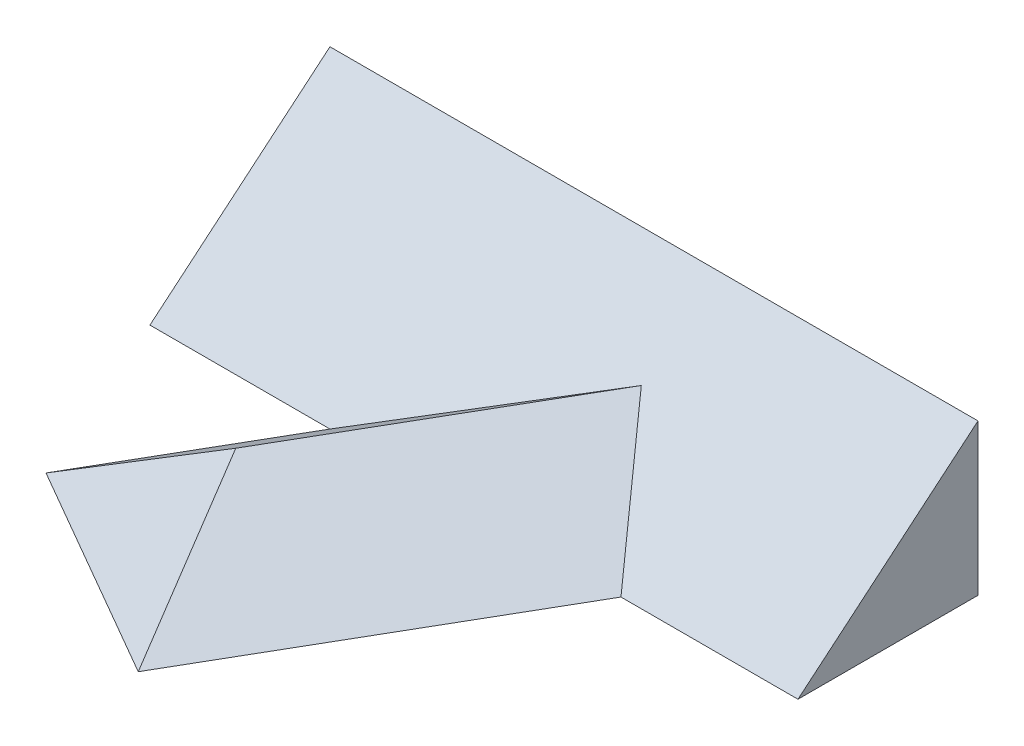
SolidWorks part; units mm, degrees
ref_plane "Front" through (0, 0, 0) normal (0, 0, 1) x (1, 0, 0)
ref_plane "Top" through (0, 0, 0) normal (0, 1, 0) x (1, 0, 0)
ref_plane "Right" through (0, 0, 0) normal (1, 0, 0) x (0, 0, -1)
sketch "Sketch1" plane through (0, 0, 0) normal (1, 0, 0) x (0, 0, -1)
  line L0 (0, 0) -> (50, 0)
  line L1 (50, 0) -> (50, 41.955)
  line L2 (50, 41.955) -> (0, 0)
  dimension "D1" = 50
  dimension "D2" = 40
extrude "Extrude1" add sketch "Sketch1" along normal blind 180
sketch "Sketch2" plane through (0, 0, 0) normal (0, 1, 0) x (1, 0, 0)
  line L0 (50, 50) -> (50, -28.1305) construction
  line L1 (180, 50) -> (0, 50) construction
  line L2 (0, 50) -> (0, 0) construction
  line L3 (50, 0) -> (10.2784, -68.7999) construction
  line L4 (180, 0) -> (0, 0) construction
  line L5 (11.5393, -44.4614) -> (81.7543, -85) construction
  line L6 (81.7543, -85) -> (130.829, 0) construction
  point P14 (21.1325, -50)
  dimension "D1" = 50
  dimension "D2" = 60
  dimension "D3" = 50
ref_plane "Plane3" through (0, 0, 50) normal (0, 0, 1) x (1, 0, 0)
sketch "Sketch4" plane through (0, 0, 50) normal (0, 0, 1) x (1, 0, 0)
  point P0 (21.1325, 31.1469)
ref_plane "Plane4" through (-16.3675, 0, 28.3494) normal (-0.5, 0, 0.866) x (0.866, 0, 0.5)
sketch "Sketch5" plane through (-16.3675, 0, 28.3494) normal (-0.5, 0, 0.866) x (0.866, 0, 0.5)
  line L0 (43.3013, 0) -> (78.3013, 24.5073)
  line L1 (78.3013, 24.5073) -> (113.3013, 0)
  line L2 (155.8846, 0) -> (0, 0) construction
  line L3 (113.3013, 0) -> (43.3013, 0)
  dimension "D1" = 70
  dimension "D2" = 35
  dimension "D3" = 35
extrude "Extrude2" add sketch "Sketch5" against normal blind 115
ref_plane "Plane5" through (51.4434, 0, 67.5) normal (0.866, 0, 0.5) x (0.5, 0, -0.866)
sketch "Sketch6" plane through (51.4434, 0, 67.5) normal (0.866, 0, 0.5) x (0.5, 0, -0.866)
  line L0 (29.2066, 24.5073) -> (0, 24.5073)
  line L1 (111.6672, 24.5073) -> (0, 24.5073) construction
  line L2 (0, 24.5073) -> (0, 0)
  line L3 (0, 0) -> (29.2066, 24.5073)
  line L4 (98.1495, 0) -> (0, 0) construction
  dimension "D1" = 40
extrude "Cut-Extrude1" cut sketch "Sketch6" against normal mid plane 70
ref_plane "AD Dihedral Angle Plane" through (43.5896, 12.2536, 46.1032) normal (-0.8678, -0.4735, 0.1506) x (0.1322, 0.0721, 0.9886)
